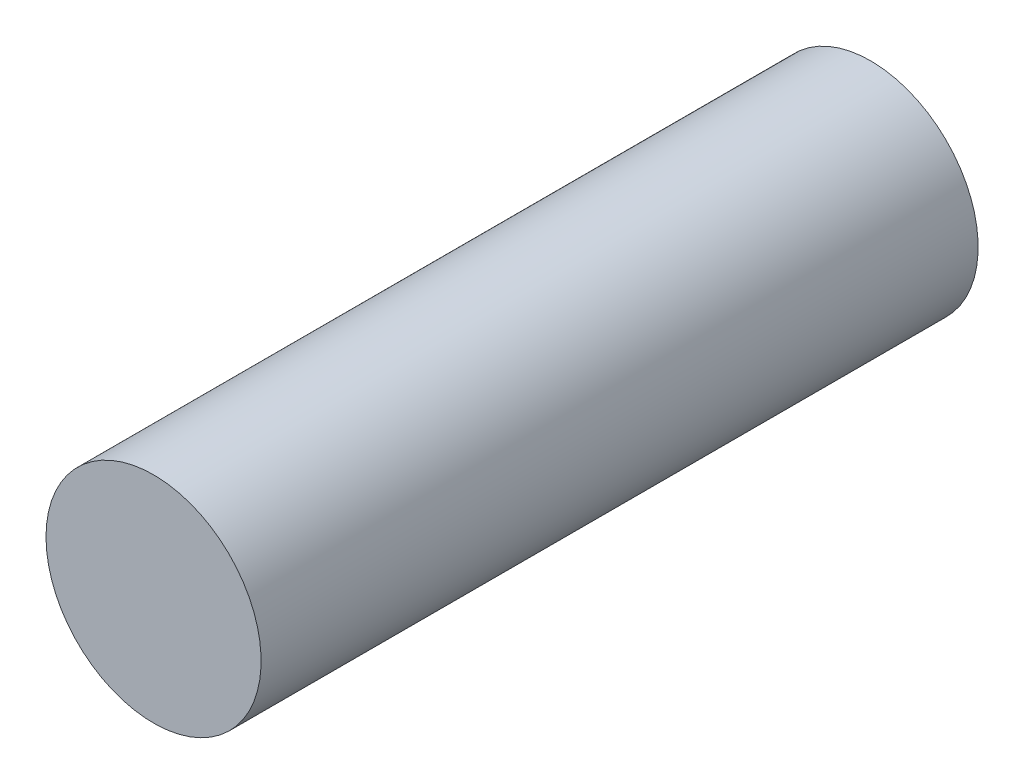
SolidWorks part; units mm, degrees
material "Wrought Stainless Steel"
ref_plane "Front Plane" through (0, 0, 0) normal (0, 0, 1) x (1, 0, 0)
ref_plane "Top Plane" through (0, 0, 0) normal (0, 1, 0) x (1, 0, 0)
ref_plane "Right Plane" through (0, 0, 0) normal (1, 0, 0) x (0, 0, -1)
sketch "Sketch1" plane through (0, 0, -90.8884) normal (0, 0, -1) x (-1, 0, 0)
  circle A0 centre (-436.19, 444.5239) radius 150
  dimension "D1" = 300
extrude "Boss-Extrude1" add sketch "Sketch1" against normal blind 1000
